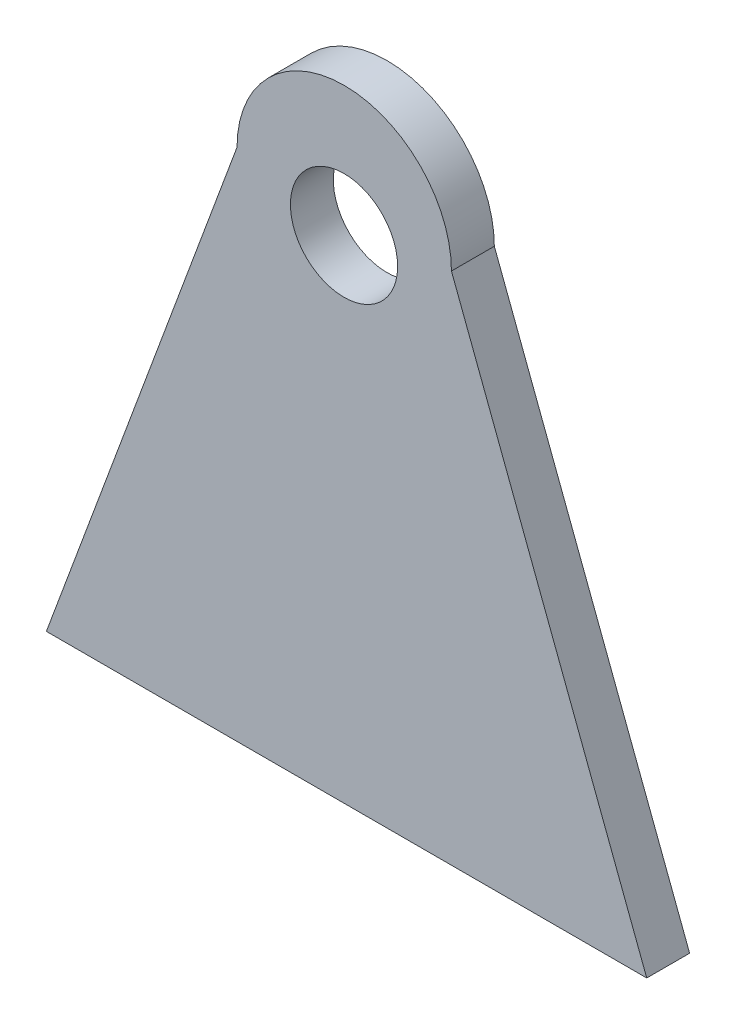
SolidWorks part; units mm, degrees
ref_plane "Front" through (0, 0, 0) normal (0, 0, 1) x (1, 0, 0)
ref_plane "Top" through (0, 0, 0) normal (0, 1, 0) x (1, 0, 0)
ref_plane "Right" through (0, 0, 0) normal (1, 0, 0) x (0, 0, -1)
sketch "Sketch1" plane through (0, 0, 0) normal (0, 0, 1) x (1, 0, 0)
  line L0 (0, 0) -> (280, 0)
  line L2 (88.9173, 240) -> (0, 0)
  line L3 (188.9173, 240) -> (280, 0)
  circle A1 centre (138.9173, 240) radius 50
  point P5 (0, 0)
  point P6 (140, 0)
  point P8 (0, 0)
  dimension "D3" = 280
  dimension "D2" = 100
  dimension "D1" = 100
extrude "Boss-Extrude2" add sketch "Sketch1" along normal blind 20 contours A1 L2 L0 L3 | A1
sketch "Sketch2" plane through (0, 0, 20) normal (0, 0, 1) x (1, 0, 0)
  circle A0 centre (138.8148, 229.349) radius 25
  dimension "D1" = 50
extrude "Cut-Extrude1" cut sketch "Sketch2" against normal blind 20
